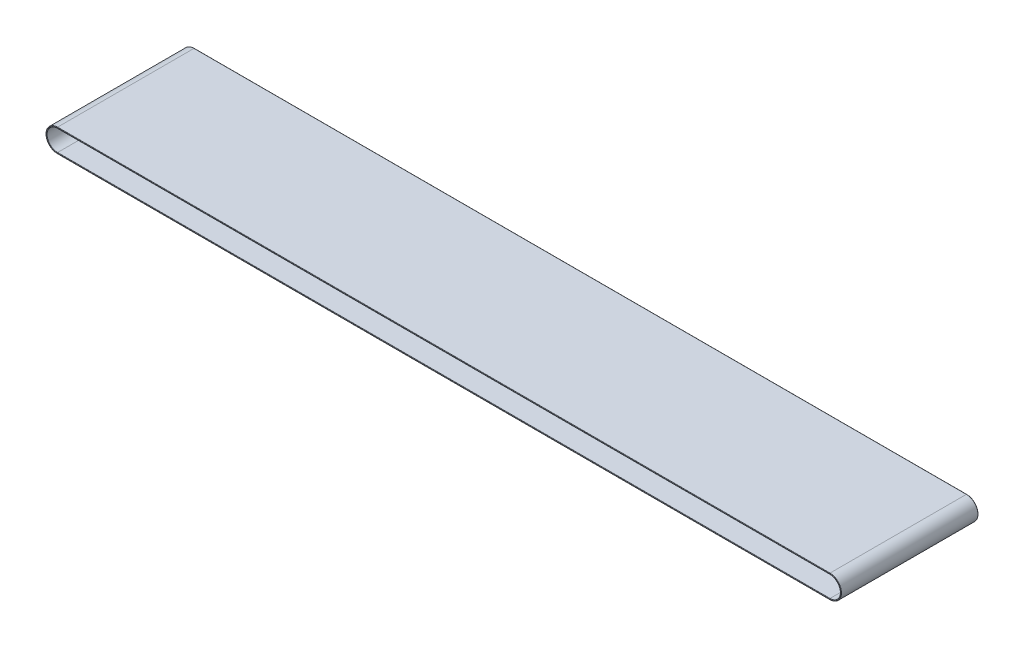
SolidWorks part; units mm, degrees
ref_plane "Front Plane" through (0, 0, 0) normal (0, 0, 1) x (1, 0, 0)
ref_plane "Top Plane" through (0, 0, 0) normal (0, 1, 0) x (1, 0, 0)
ref_plane "Right Plane" through (0, 0, 0) normal (1, 0, 0) x (0, 0, -1)
sketch "Sketch2" plane through (0, 0, 0) normal (0, 0, 1) x (1, 0, 0)
  line L0 (-142.875, 3.8735) -> (142.875, 3.8735)
  line L1 (-142.875, 2.54) -> (142.875, 2.54)
  line L2 (-142.875, 2.54) -> (-142.875, -2.54)
  line L3 (-142.875, -2.54) -> (142.875, -2.54)
  line L4 (142.875, 2.54) -> (142.875, -2.54)
  line L5 (-142.875, 2.54) -> (142.875, -2.54) construction
  line L6 (-142.875, -2.54) -> (142.875, 2.54) construction
  line L7 (-142.875, -3.8735) -> (142.875, -3.8735)
  line L8 (-142.875, 4.2545) -> (142.875, 4.2545)
  line L9 (-142.875, -4.2545) -> (142.875, -4.2545)
  arc A1 (-142.875, 3.8735) -> (-142.875, -3.8735) centre (-142.875, 0) ccw
  arc A2 (139.9506, 2.54) -> (139.9506, -2.54) centre (142.875, 0) ccw
  arc A3 (-139.9506, -2.54) -> (-139.9506, 2.54) centre (-142.875, 0) ccw
  arc A4 (142.875, -3.8735) -> (142.875, 3.8735) centre (142.875, 0) ccw
  arc A5 (142.875, -4.2545) -> (142.875, 4.2545) centre (142.875, 0) ccw
  arc A6 (-142.875, 4.2545) -> (-142.875, -4.2545) centre (-142.875, 0) ccw
  point P0 (0, 0)
  point P9 (-142.875, 0)
  point P13 (142.875, 0)
  dimension "D3" = 7.747
  dimension "D4" = 7.747
  dimension "D1" = 5.08
  dimension "D2" = 285.75
  dimension "D5" = 0.381
  dimension "D6" = 7.747
extrude "Boss-Extrude1" add sketch "Sketch2" along normal blind 50.673 contours L8 A6 L9 A5 A4 L7 A1 L0
fillet "Fillet1" radius 0.127 16 edges at (-147.1295, 0, 50.673) (0, -4.2545, 50.673) (147.1295, 0, 50.673) (0, 4.2545, 50.673) (-146.7485, 0, 50.673) (0, -3.8735, 50.673) (146.7485, 0, 50.673) (0, 3.8735, 50.673) (-146.7485, 0, 0) (0, -3.8735, 0) (146.7485, 0, 0) (-147.1295, 0, 0) (0, -4.2545, 0) (147.1295, 0, 0) (0, 3.8735, 0) (0, 4.2545, 0)
